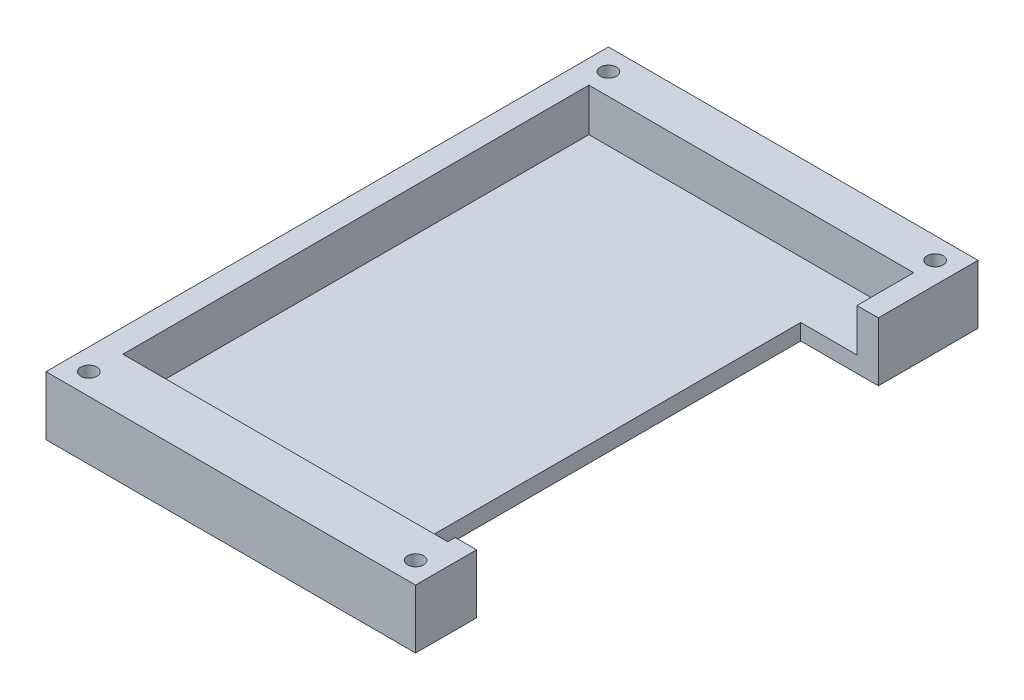
SolidWorks part; units mm, degrees
ref_plane "Front Plane" through (0, 0, 0) normal (0, 0, 1) x (1, 0, 0)
ref_plane "Top Plane" through (0, 0, 0) normal (0, 1, 0) x (1, 0, 0)
ref_plane "Right Plane" through (0, 0, 0) normal (1, 0, 0) x (0, 0, -1)
sketch "Sketch1" plane through (0, 0, 0) normal (0, 1, 0) x (1, 0, 0)
  line L1 (0, 0) -> (69, 0)
  line L2 (0, 0) -> (0, 105)
  line L3 (0, 105) -> (69, 105)
  line L4 (69, 0) -> (69, 105)
  dimension "D1" = 105
  dimension "D2" = 69
extrude "Boss-Extrude2" add sketch "Sketch1" along normal blind 11
sketch "Sketch3" plane through (0, 11, 0) normal (0, 1, 0) x (1, 0, 0)
  line L0 (69, 0) -> (69, 105) construction
  line L1 (4.358, 97) -> (65, 97)
  line L2 (4.358, 97) -> (4.358, 10)
  line L3 (4.358, 10) -> (65, 10)
  line L4 (65, 97) -> (65, 10)
  line L5 (69, 105) -> (0, 105) construction
  line L6 (0, 0) -> (69, 0) construction
  dimension "D1" = 4
  dimension "D2" = 8
  dimension "D3" = 10
extrude "Cut-Extrude1" cut sketch "Sketch3" against normal blind 8
sketch "Sketch4" plane through (0, 11, 0) normal (0, 1, 0) x (1, 0, 0)
  line L0 (0, 0) -> (69, 0) construction
  line L1 (0, 105) -> (0, 0) construction
  line L2 (69, 0) -> (69, 105) construction
  line L3 (69, 105) -> (0, 105) construction
  circle A0 centre (4, 101) radius 1.5
  circle A1 centre (65, 101) radius 1.5
  circle A2 centre (4, 4) radius 1.5
  circle A3 centre (65, 4) radius 1.5
  dimension "D1" = 3
  dimension "D2" = 3
  dimension "D3" = 3
  dimension "D4" = 3
  dimension "D5" = 4
  dimension "D6" = 4
  dimension "D7" = 4
  dimension "D8" = 4
  dimension "D9" = 4
  dimension "D10" = 4
  dimension "D11" = 4
  dimension "D12" = 4
extrude "Cut-Extrude2" cut sketch "Sketch4" against normal through all
sketch "Sketch5" plane through (0, 11, 0) normal (0, 1, 0) x (1, 0, 0)
  line L1 (69, 0) -> (69, 105) construction
  line L2 (69, 86.4) -> (54.5, 86.4)
  line L3 (69, 86.4) -> (69, 11.4)
  line L4 (69, 11.4) -> (54.5, 11.4)
  line L7 (54.5, 86.4) -> (54.5, 11.4)
  line L8 (4.358, 10) -> (65, 10) construction
  dimension "D1" = 14.5
  dimension "D2" = 1.4
  dimension "D3" = 75
extrude "Cut-Extrude3" cut sketch "Sketch5" against normal through all
